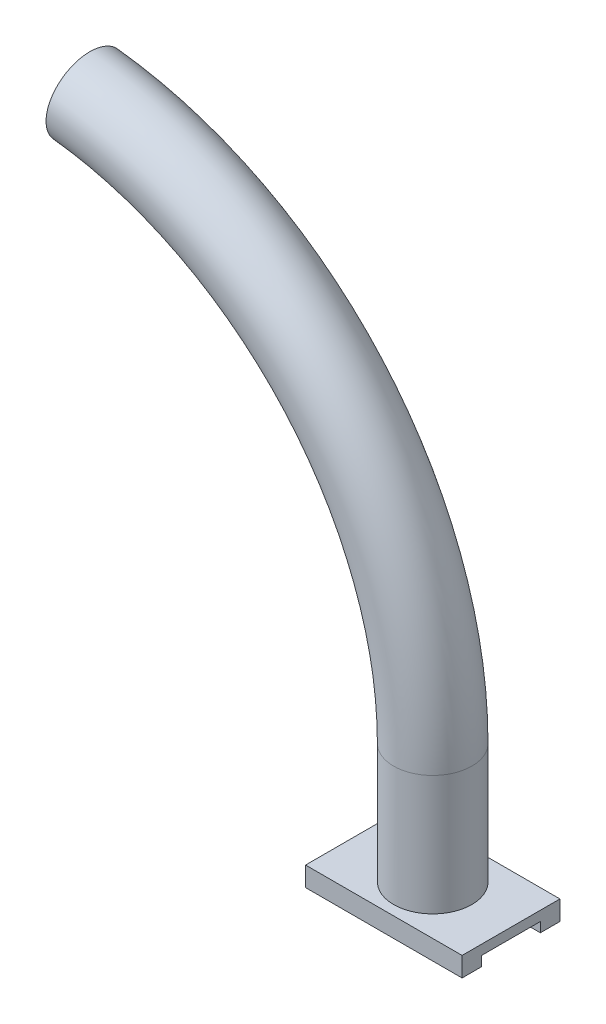
SolidWorks part; units mm, degrees
ref_plane "Front Plane" through (0, 0, 0) normal (0, 0, 1) x (1, 0, 0)
ref_plane "Top Plane" through (0, 0, 0) normal (0, 1, 0) x (1, 0, 0)
ref_plane "Right Plane" through (0, 0, 0) normal (1, 0, 0) x (0, 0, -1)
sketch "Sketch1" plane through (0, 0, 0) normal (0, 1, 0) x (1, 0, 0)
  line L1 (0, 0) -> (8, 0)
  line L2 (0, 0) -> (0, 5)
  line L3 (0, 5) -> (8, 5)
  line L4 (8, 0) -> (8, 5)
  dimension "D1" = 5
  dimension "D2" = 8
extrude "Boss-Extrude1" add sketch "Sketch1" along normal blind 0.5
sketch "Sketch2" plane through (0, 0, 0) normal (0, -1, 0) x (1, 0, 0)
  line L0 (8, 0) -> (8, -5) construction
  line L1 (0, 0) -> (8, 0)
  line L2 (0, 0) -> (0, -1)
  line L3 (0, -1) -> (8, -1)
  line L4 (8, 0) -> (8, -1)
  line L5 (0, -5) -> (0, 0) construction
  line L6 (0, -4) -> (8, -4)
  line L7 (0, -4) -> (0, -5)
  line L8 (0, -5) -> (8, -5)
  line L9 (8, -4) -> (8, -5)
  dimension "D1" = 1
  dimension "D2" = 1
extrude "Boss-Extrude2" add sketch "Sketch2" along normal blind 0.5
sketch "Sketch3" plane through (0, 0.5, 0) normal (0, 1, 0) x (1, 0, 0)
  line L0 (-8, 10) -> (8, 0) construction
  line L2 (-8, -5) -> (8, 5) construction
  line L3 (8, 5) -> (0, 5) construction
  circle A0 centre (4, 2.5) radius 2
  point P0 (4, 2.5)
  point P4 (0, 5)
  point P12 (0, 0)
  dimension "D1" = 4
extrude "Boss-Extrude3" add sketch "Sketch3" along normal blind 1
sketch "Sketch4" plane through (0, 1.5, 0) normal (0, 1, 0) x (1, 0, 0)
  line L0 (2, 2.5) -> (6, 2.5) construction
  circle A0 centre (4, 2.5) radius 2 construction
  circle A1 centre (4, 2.5) radius 2 construction
ref_plane "Plane1" through (0, 0, -2.5) normal (0, 0, 1) x (1, 0, 0)
sketch "Sketch6" plane through (0, 0, -2.5) normal (0, 0, 1) x (1, 0, 0)
  line L3 (4, 6.627) -> (4, 1.5)
  line L4 (2, 1.5) -> (6, 1.5) construction
  arc A0 (4, 6.627) -> (-13.7501, 26.5) centre (-16, 6.627) ccw
  dimension "D1" = 20
  dimension "D2" = 25
sweep "Sweep5" add path "Sketch6" circular profile diameter 4 parameters "D3"=4
